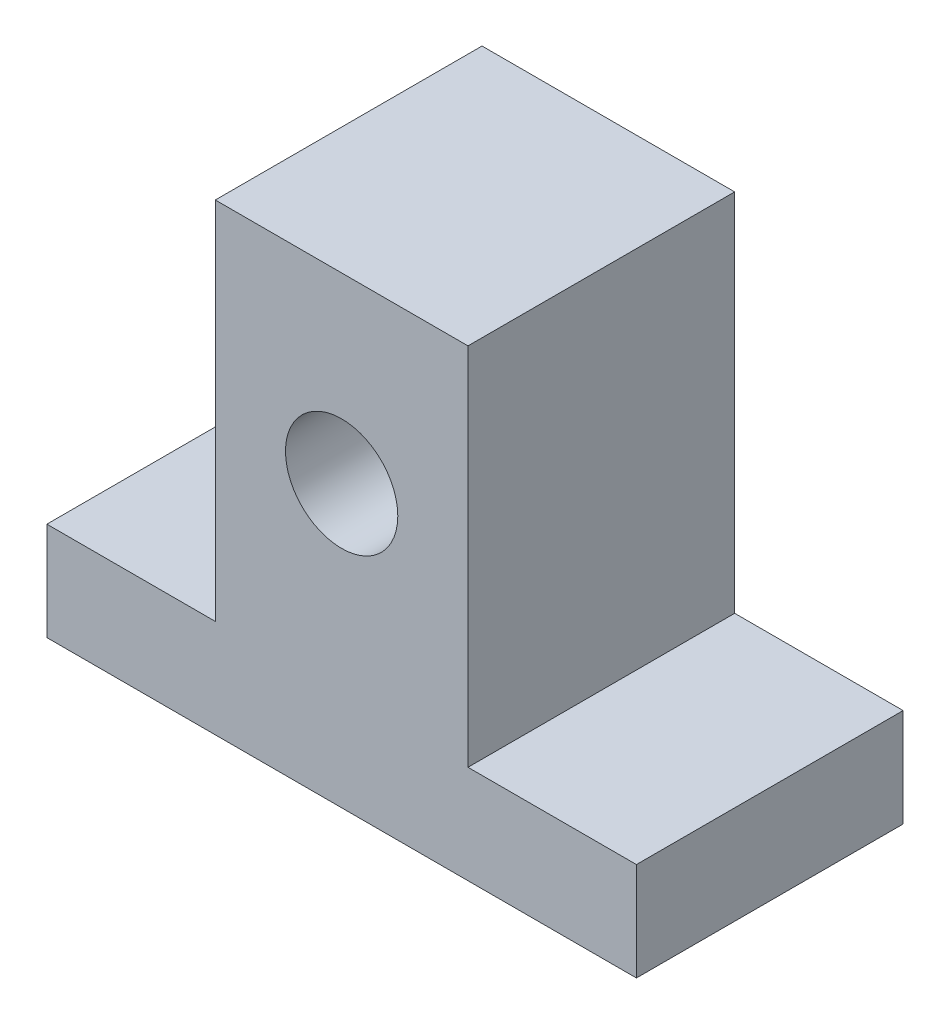
SolidWorks part; units mm, degrees
material "Plain Carbon Steel"
ref_plane "Front Plane" through (0, 0, 0) normal (0, 0, 1) x (1, 0, 0)
ref_plane "Top Plane" through (0, 0, 0) normal (0, 1, 0) x (1, 0, 0)
ref_plane "Right Plane" through (0, 0, 0) normal (1, 0, 0) x (0, 0, -1)
sketch "Sketch2" plane through (0, 0, 0) normal (0, 0, 1) x (1, 0, 0)
  line L0 (0, 0) -> (0, 38.9118) construction
  line L1 (-21, 0) -> (21, 0)
  line L2 (21, 0) -> (21, 7)
  line L3 (21, 7) -> (9, 7)
  line L4 (9, 7) -> (9, 33)
  line L5 (9, 33) -> (-9, 33)
  line L6 (-9, 33) -> (-9, 7)
  line L7 (-9, 7) -> (-21, 7)
  line L8 (-21, 7) -> (-21, 0)
  line L9 (-21, 0) -> (-20.9633, 0.2748)
  circle A0 centre (0, 20) radius 4
  dimension "D7" = 20
  dimension "D8" = 8
  dimension "D1" = 42
  dimension "D2" = 9
  dimension "D3" = 9
  dimension "D4" = 7
  dimension "D5" = 7
  dimension "D6" = 33
extrude "Boss-Extrude1" add sketch "Sketch2" along normal blind 19
